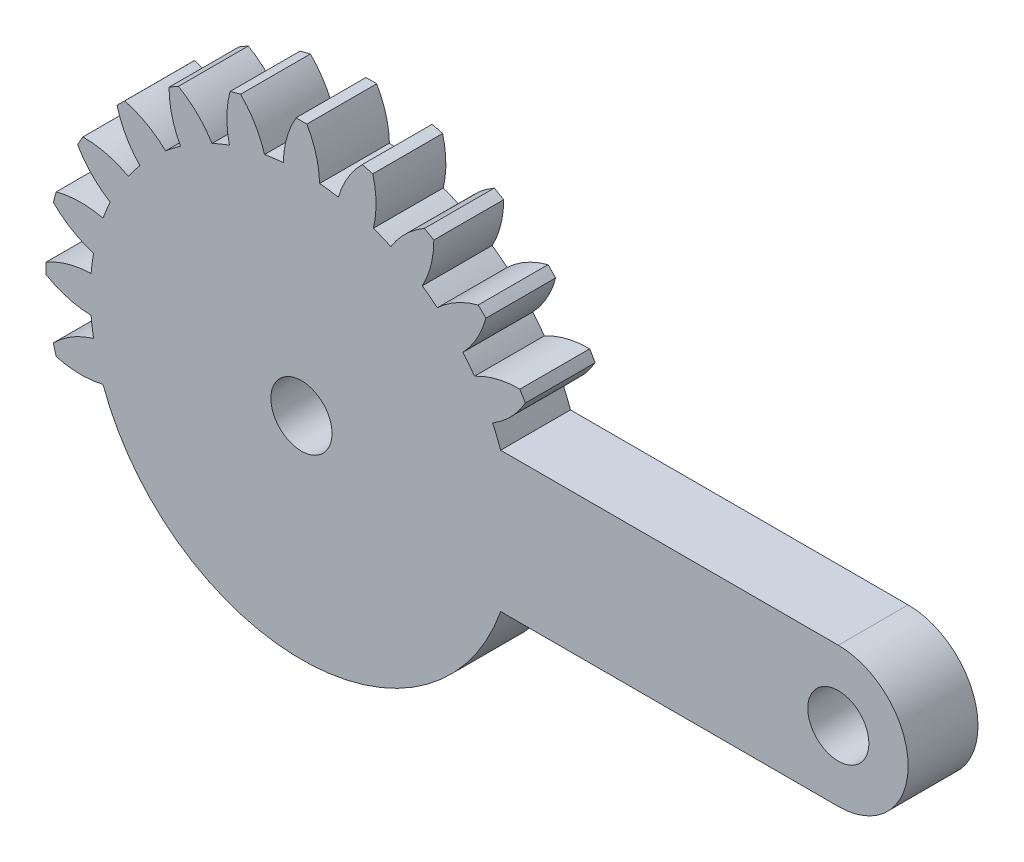
SolidWorks part; units mm, degrees
material "ABS"
ref_plane "Plan de face" through (0, 0, 0) normal (0, 0, 1) x (1, 0, 0)
ref_plane "Plan de dessus" through (0, 0, 0) normal (0, 1, 0) x (1, 0, 0)
ref_plane "Plan de droite" through (0, 0, 0) normal (1, 0, 0) x (0, 0, -1)
sketch "Esquisse1" plane through (0, 0, 0) normal (0, 0, 1) x (1, 0, 0)
  line L0 (0, 0) -> (0, 14.63) construction
  line L1 (0, 0) -> (30.75, 0) construction
  line L2 (14.0726, 4) -> (30.75, 4)
  line L3 (11.4091, -4) -> (30.75, -4)
  line L4 (14.0726, 4) -> (11.4091, 4)
  circle A0 centre (0, 0) radius 1.75
  circle A1 centre (0, 0) radius 12.09
  arc A2 (14.0726, -4) -> (14.0726, 4) centre (0, 0) ccw
  arc A3 (-0.31, 14.6267) -> (-1.04, 12.0452) centre (4.3584, 11.9126) ccw
  arc A4 (0.31, 14.6267) -> (1.04, 12.0452) centre (-4.3584, 11.9126) cw
  arc A5 (0.31, 14.6267) -> (-0.31, 14.6267) centre (0, 0) ccw
  arc A6 (4.0851, 14.0481) -> (4.1221, 11.3656) centre (-1.1267, 12.6347) cw
  arc A7 (3.4862, 14.2086) -> (2.113, 11.9039) centre (7.2931, 10.3787) ccw
  arc A8 (4.0851, 14.0481) -> (3.4862, 14.2086) centre (0, 0) ccw
  arc A9 (7.5818, 12.5121) -> (6.9233, 9.9114) centre (2.1819, 12.4958) cw
  arc A10 (7.0449, 12.8221) -> (5.1219, 10.9514) centre (9.7308, 8.1374) ccw
  arc A11 (7.5818, 12.5121) -> (7.0449, 12.8221) centre (0, 0) ccw
  arc A12 (10.5619, 10.1234) -> (9.2526, 7.7818) centre (5.3417, 11.5053) cw
  arc A13 (10.1234, 10.5619) -> (7.7818, 9.2526) centre (11.5053, 5.3417) ccw
  arc A14 (10.5619, 10.1234) -> (10.1234, 10.5619) centre (0, 0) ccw
  arc A15 (12.8221, 7.0449) -> (10.9514, 5.1219) centre (8.1374, 9.7308) cw
  arc A16 (12.5121, 7.5818) -> (9.9114, 6.9233) centre (12.4958, 2.1819) ccw
  arc A17 (12.8221, 7.0449) -> (12.5121, 7.5818) centre (0, 0) ccw
  arc A18 (14.2086, 3.4862) -> (11.9039, 2.113) centre (10.3787, 7.2931) cw
  arc A19 (14.0481, 4.0851) -> (11.3656, 4.1221) centre (12.6347, -1.1267) ccw
  arc A20 (14.2086, 3.4862) -> (14.0481, 4.0851) centre (0, 0) ccw
  arc A21 (14.6267, -0.31) -> (12.0452, -1.04) centre (11.9126, 4.3584) cw
  arc A22 (14.6267, 0.31) -> (12.0452, 1.04) centre (11.9126, -4.3584) ccw
  arc A23 (14.6267, -0.31) -> (14.6267, 0.31) centre (0, 0) ccw
  arc A24 (14.0481, -4.0851) -> (11.3656, -4.1221) centre (12.6347, 1.1267) cw
  arc A25 (14.2086, -3.4862) -> (11.9039, -2.113) centre (10.3787, -7.2931) ccw
  arc A26 (14.0481, -4.0851) -> (14.2086, -3.4862) centre (0, 0) ccw
  arc A27 (12.5121, -7.5818) -> (9.9114, -6.9233) centre (12.4958, -2.1819) cw
  arc A28 (12.8221, -7.0449) -> (10.9514, -5.1219) centre (8.1374, -9.7308) ccw
  arc A29 (12.5121, -7.5818) -> (12.8221, -7.0449) centre (0, 0) ccw
  arc A30 (10.1234, -10.5619) -> (7.7818, -9.2526) centre (11.5053, -5.3417) cw
  arc A31 (10.5619, -10.1234) -> (9.2526, -7.7818) centre (5.3417, -11.5053) ccw
  arc A32 (10.1234, -10.5619) -> (10.5619, -10.1234) centre (0, 0) ccw
  arc A33 (7.0449, -12.8221) -> (5.1219, -10.9514) centre (9.7308, -8.1374) cw
  arc A34 (7.5818, -12.5121) -> (6.9233, -9.9114) centre (2.1819, -12.4958) ccw
  arc A35 (7.0449, -12.8221) -> (7.5818, -12.5121) centre (0, 0) ccw
  arc A36 (3.4862, -14.2086) -> (2.113, -11.9039) centre (7.2931, -10.3787) cw
  arc A37 (4.0851, -14.0481) -> (4.1221, -11.3656) centre (-1.1267, -12.6347) ccw
  arc A38 (3.4862, -14.2086) -> (4.0851, -14.0481) centre (0, 0) ccw
  arc A39 (-0.31, -14.6267) -> (-1.04, -12.0452) centre (4.3584, -11.9126) cw
  arc A40 (0.31, -14.6267) -> (1.04, -12.0452) centre (-4.3584, -11.9126) ccw
  arc A41 (-0.31, -14.6267) -> (0.31, -14.6267) centre (0, 0) ccw
  arc A42 (-4.0851, -14.0481) -> (-4.1221, -11.3656) centre (1.1267, -12.6347) cw
  arc A43 (-3.4862, -14.2086) -> (-2.113, -11.9039) centre (-7.2931, -10.3787) ccw
  arc A44 (-4.0851, -14.0481) -> (-3.4862, -14.2086) centre (0, 0) ccw
  arc A45 (-7.5818, -12.5121) -> (-6.9233, -9.9114) centre (-2.1819, -12.4958) cw
  arc A46 (-7.0449, -12.8221) -> (-5.1219, -10.9514) centre (-9.7308, -8.1374) ccw
  arc A47 (-7.5818, -12.5121) -> (-7.0449, -12.8221) centre (0, 0) ccw
  arc A48 (-10.5619, -10.1234) -> (-9.2526, -7.7818) centre (-5.3417, -11.5053) cw
  arc A49 (-10.1234, -10.5619) -> (-7.7818, -9.2526) centre (-11.5053, -5.3417) ccw
  arc A50 (-10.5619, -10.1234) -> (-10.1234, -10.5619) centre (0, 0) ccw
  arc A51 (30.75, 4) -> (30.75, -4) centre (30.75, 0) cw
  circle A52 centre (30.75, 0) radius 1.75
  arc A56 (-12.8221, -7.0449) -> (-10.9514, -5.1219) centre (-8.1374, -9.7308) cw
  arc A57 (-12.5121, -7.5818) -> (-9.9114, -6.9233) centre (-12.4958, -2.1819) ccw
  arc A58 (-12.8221, -7.0449) -> (-12.5121, -7.5818) centre (0, 0) ccw
  arc A59 (-14.2086, -3.4862) -> (-11.9039, -2.113) centre (-10.3787, -7.2931) cw
  arc A60 (-14.0481, -4.0851) -> (-11.3656, -4.1221) centre (-12.6347, 1.1267) ccw
  arc A61 (-14.2086, -3.4862) -> (-14.0481, -4.0851) centre (0, 0) ccw
  arc A62 (-14.6267, 0.31) -> (-12.0452, 1.04) centre (-11.9126, -4.3584) cw
  arc A63 (-14.6267, -0.31) -> (-12.0452, -1.04) centre (-11.9126, 4.3584) ccw
  arc A64 (-14.6267, 0.31) -> (-14.6267, -0.31) centre (0, 0) ccw
  arc A65 (-14.0481, 4.0851) -> (-11.3656, 4.1221) centre (-12.6347, -1.1267) cw
  arc A66 (-14.2086, 3.4862) -> (-11.9039, 2.113) centre (-10.3787, 7.2931) ccw
  arc A67 (-14.0481, 4.0851) -> (-14.2086, 3.4862) centre (0, 0) ccw
  arc A68 (-12.5121, 7.5818) -> (-9.9114, 6.9233) centre (-12.4958, 2.1819) cw
  arc A69 (-12.8221, 7.0449) -> (-10.9514, 5.1219) centre (-8.1374, 9.7308) ccw
  arc A70 (-12.5121, 7.5818) -> (-12.8221, 7.0449) centre (0, 0) ccw
  arc A71 (-10.1234, 10.5619) -> (-7.7818, 9.2526) centre (-11.5053, 5.3417) cw
  arc A72 (-10.5619, 10.1234) -> (-9.2526, 7.7818) centre (-5.3417, 11.5053) ccw
  arc A73 (-10.1234, 10.5619) -> (-10.5619, 10.1234) centre (0, 0) ccw
  arc A74 (-7.0449, 12.8221) -> (-5.1219, 10.9514) centre (-9.7308, 8.1374) cw
  arc A75 (-7.5818, 12.5121) -> (-6.9233, 9.9114) centre (-2.1819, 12.4958) ccw
  arc A76 (-7.0449, 12.8221) -> (-7.5818, 12.5121) centre (0, 0) ccw
  arc A77 (-3.4862, 14.2086) -> (-2.113, 11.9039) centre (-7.2931, 10.3787) cw
  arc A78 (-4.0851, 14.0481) -> (-4.1221, 11.3656) centre (1.1267, 12.6347) ccw
  arc A79 (-3.4862, 14.2086) -> (-4.0851, 14.0481) centre (0, 0) ccw
  point P152 (0, 0)
  point P171 (0, 0)
  dimension "D1" = 3.5
  dimension "D2" = 24.18
  dimension "D3" = 29.26
  dimension "D6" = 5.4
  dimension "D8" = 4
  dimension "D10" = 3.5
  dimension "D4" = 0.62
  dimension "D5" = 2.08
  dimension "D9" = 30.75
  dimension "D7" = 24
extrude "Boss.-Extru.1" add sketch "Esquisse1" along normal mid plane 4 contours A1 | A51 L2 A2 L3 A52 | A22 A2 A18 A1 | A18 A2 L4 A1 | A2 A25 A1 L3 | A25 A2 A21 A1 | A2 A22 A1 A21 | A15 A17 A16 A1 | A12 A14 A13 A1 | A9 A11 A10 A1 | A6 A8 A7 A1 | A4 A5 A3 A1 | A77 A79 A78 A1 | A74 A76 A75 A1 | A71 A73 A72 A1 | A68 A70 A69 A1 | A65 A67 A66 A1 | A62 A64 A63 A1 | A59 A61 A60 A1
